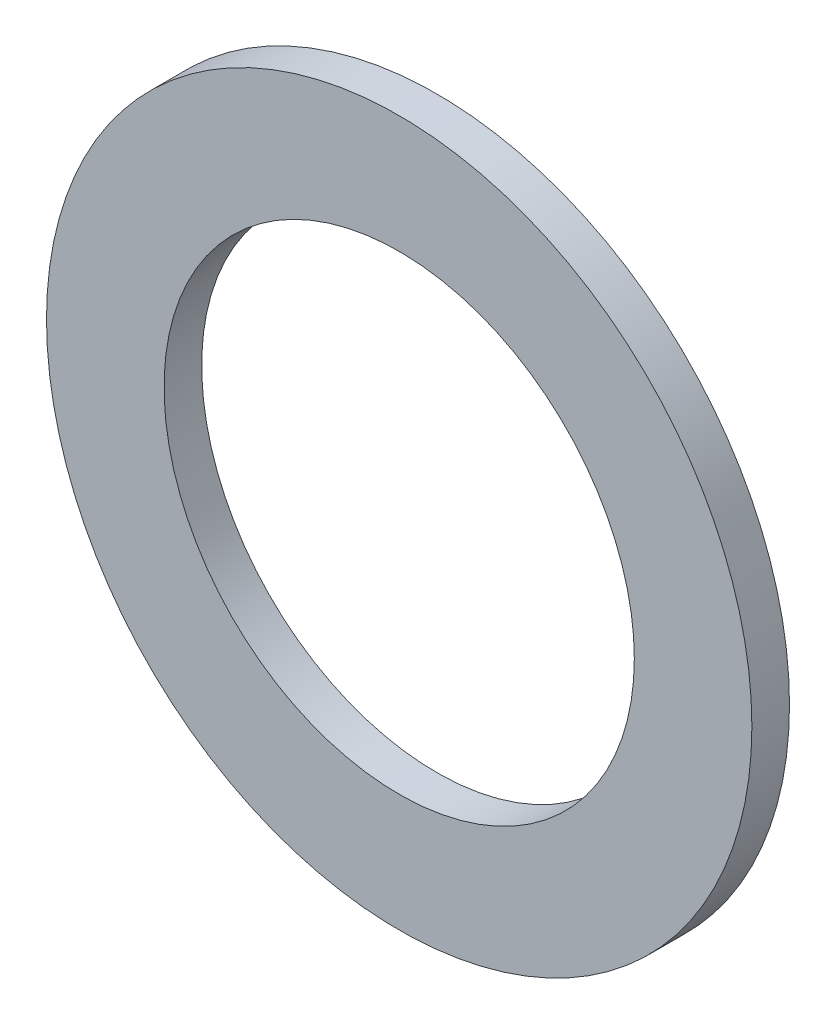
SolidWorks part; units mm, degrees
material "Plain Carbon Steel"
ref_plane "Front Plane" through (0, 0, 0) normal (0, 0, 1) x (1, 0, 0)
ref_plane "Top Plane" through (0, 0, 0) normal (0, 1, 0) x (1, 0, 0)
ref_plane "Right Plane" through (0, 0, 0) normal (1, 0, 0) x (0, 0, -1)
sketch "Sketch1" plane through (0, 0, 0) normal (0, 0, 1) x (1, 0, 0)
  circle A0 centre (0, 0) radius 2.3813
  circle A1 centre (0, 0) radius 1.5875
  dimension "D1" = 4.7625
  dimension "D2" = 3.175
extrude "Boss-Extrude1" add sketch "Sketch1" along normal mid plane 0.254
